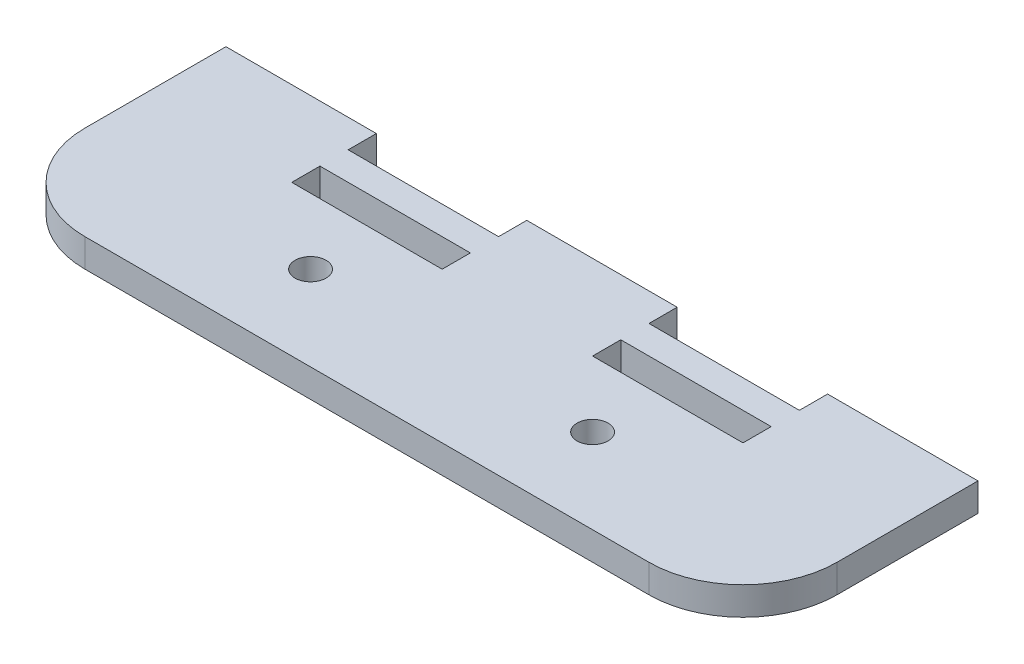
SolidWorks part; units mm, degrees
ref_plane "Ön Düzlem" through (0, 0, 0) normal (0, 0, 1) x (1, 0, 0)
ref_plane "Üst Düzlem" through (0, 0, 0) normal (0, 1, 0) x (1, 0, 0)
ref_plane "Sağ Düzlem" through (0, 0, 0) normal (1, 0, 0) x (0, 0, -1)
sketch "Sketch1" plane through (0, 0, 0) normal (0, 1, 0) x (1, 0, 0)
  line L0 (-40, 12.5) -> (-40, 9.5) construction
  line L1 (30, -12.5) -> (-30, -12.5)
  line L2 (40, -2.5) -> (40, 12.5)
  line L3 (40, 12.5) -> (24, 12.5)
  line L4 (-40, -2.5) -> (-40, 12.5)
  line L5 (40, -12.5) -> (0, 0) construction
  line L6 (40, 12.5) -> (-40, -12.5) construction
  line L7 (-40, 9.5) -> (-40, 5.8835) construction
  line L8 (-40, 5.8835) -> (-40, 3.2973) construction
  line L9 (-24, 6.5) -> (-24, 3.5)
  line L10 (-24, 3.5) -> (-8, 3.5)
  line L11 (-40, 9.5) -> (40, 9.5) construction
  line L12 (-40, 9.5) -> (-24, 9.5) construction
  line L13 (-24, 9.5) -> (-24, 12.5)
  line L14 (-24, 9.5) -> (-8, 9.5)
  line L15 (-8, 9.5) -> (-8, 12.5)
  line L16 (40, 9.5) -> (24, 9.5) construction
  line L17 (24, 9.5) -> (24, 12.5)
  line L18 (24, 9.5) -> (8, 9.5)
  line L19 (8, 9.5) -> (8, 12.5)
  line L20 (-24, 12.5) -> (-40, 12.5)
  line L21 (8, 12.5) -> (-8, 12.5)
  line L30 (-8, 3.5) -> (-8, 6.5)
  line L31 (-24, 6.5) -> (-8, 6.5)
  line L32 (8, 6.5) -> (8, 3.5)
  line L33 (8, 6.5) -> (24, 6.5)
  line L34 (8, 3.5) -> (24, 3.5)
  line L35 (-18.8274, 5.8835) -> (-40, 12.5) construction
  line L36 (24, 3.5) -> (24, 6.5)
  circle A0 centre (-15, -3.5) radius 1.65
  circle A1 centre (15, -3.5) radius 1.65
  arc A2 (-40, -2.5) -> (-30, -12.5) centre (-30, -2.5) ccw
  arc A3 (40, -2.5) -> (30, -12.5) centre (30, -2.5) cw
  point P0 (0, 0)
  dimension "D3" = 10
  dimension "D4" = 10
  dimension "D5" = 16
  dimension "D6" = 16
  dimension "D1" = 25
  dimension "D2" = 80
extrude "Boss-Extrude1" add sketch "Sketch1" along normal blind 3
